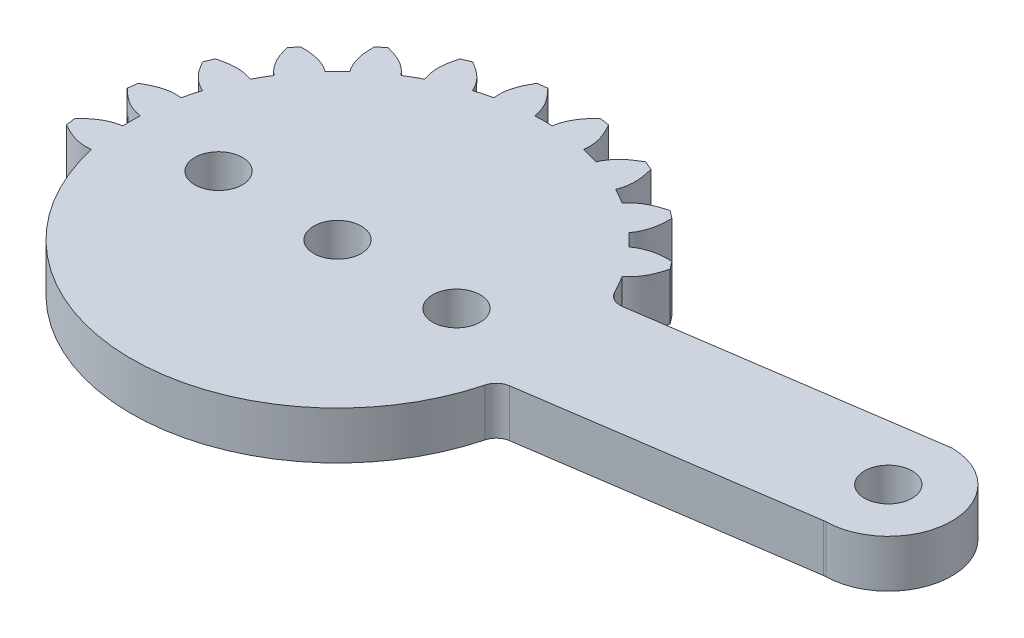
SolidWorks part; units mm, degrees
ref_plane "Front Plane" through (0, 0, 0) normal (0, 0, 1) x (1, 0, 0)
ref_plane "Top Plane" through (0, 0, 0) normal (0, 1, 0) x (1, 0, 0)
ref_plane "Right Plane" through (0, 0, 0) normal (1, 0, 0) x (0, 0, -1)
sketch "Sketch1" plane through (0, 0, 0) normal (0, 1, 0) x (1, 0, 0)
  line L0 (12.6327, 5.3405) -> (30.6525, 7.9886)
  line L1 (0, 0) -> (11.9003, 9.1314) construction
  line L2 (0, 0) -> (19.2179, 25.0452) construction
  line L3 (0, 0) -> (9.1924, 9.1924) construction
  line L5 (30.6617, -0.01) -> (13.4007, -2.5466)
  circle A2 centre (0, 0) radius 1.5
  circle A3 centre (7.5, 0) radius 1.5
  circle A4 centre (-7.5, 0) radius 1.5
  arc A5 (-12.4035, -3.8928) -> (12.5785, -3.2834) centre (0, 0) ccw
  circle A6 centre (30.73, 4) radius 1.5
  arc A8 (11.5954, 5.8777) -> (10.9732, 6.9706) centre (0, 0) ccw
  arc A9 (30.7917, 0.0005) -> (30.8205, 7.999) centre (30.73, 4) ccw
  arc A10 (30.6617, -0.01) -> (30.7917, 0.0005) centre (30.8071, -0.9994) cw
  arc A11 (30.6525, 7.9886) -> (30.8205, 7.999) centre (30.7979, 6.9992) cw
  arc A12 (12.6327, 5.3405) -> (11.5954, 5.8777) centre (12.4873, 6.3299) cw
  arc A13 (12.5785, -3.2834) -> (13.4007, -2.5466) centre (13.5461, -3.536) cw
  spline S0 degree 3 poles (9.5731, 8.7952) (10.2501, 9.2991) (10.982, 9.3793) (11.7091, 9.3754) knots 0 0 0 0 0.58557 0.58557 0.58557 0.58557
  spline S1 degree 2 poles (11.7091, 9.3754) (11.9028, 9.1334) (12.0865, 8.8835) knots 0 0 0 1 1 1
  spline S2 degree 3 poles (10.9732, 6.9706) (11.6352, 7.494) (11.9021, 8.1802) (12.0865, 8.8835) knots 0 0 0 0 0.58557 0.58557 0.58557 0.58557
  spline S4 degree 3 poles (8.7952, 9.5731) (9.2991, 10.2501) (9.3793, 10.982) (9.3754, 11.7091) knots 0 0 0 0 0.58557 0.58557 0.58557 0.58557
  spline S5 degree 2 poles (8.8835, 12.0865) (9.1334, 11.9028) (9.3754, 11.7091) knots 0 0 0 1 1 1
  spline S6 degree 3 poles (6.9706, 10.9732) (7.494, 11.6352) (8.1802, 11.9021) (8.8835, 12.0865) knots 0 0 0 0 0.58557 0.58557 0.58557 0.58557
  spline S7 degree 3 poles (6.0178, 11.5233) (6.3294, 12.3076) (6.2174, 13.0353) (6.0254, 13.7366) knots 0 0 0 0 0.58557 0.58557 0.58557 0.58557
  spline S8 degree 2 poles (5.4526, 13.9739) (5.7415, 13.8612) (6.0254, 13.7366) knots 0 0 0 1 1 1
  spline S9 degree 3 poles (3.893, 12.4034) (4.2273, 13.1783) (4.821, 13.6137) (5.4526, 13.9739) knots 0 0 0 0 0.58557 0.58557 0.58557 0.58557
  spline S10 degree 3 poles (2.8303, 12.6882) (2.9283, 13.5264) (2.6318, 14.2003) (2.2648, 14.828) knots 0 0 0 0 0.58557 0.58557 0.58557 0.58557
  spline S11 degree 2 poles (1.6501, 14.909) (1.9583, 14.8748) (2.2648, 14.828) knots 0 0 0 1 1 1
  spline S12 degree 3 poles (0.5501, 12.9884) (0.6724, 13.8234) (1.1332, 14.3976) (1.6501, 14.909) knots 0 0 0 0 0.58557 0.58557 0.58557 0.58557
  spline S13 degree 3 poles (-0.5501, 12.9884) (-0.6724, 13.8234) (-1.1332, 14.3976) (-1.6501, 14.909) knots 0 0 0 0 0.58557 0.58557 0.58557 0.58557
  spline S14 degree 2 poles (-2.2648, 14.828) (-1.9583, 14.8748) (-1.6501, 14.909) knots 0 0 0 1 1 1
  spline S15 degree 3 poles (-2.8303, 12.6882) (-2.9283, 13.5264) (-2.6318, 14.2003) (-2.2648, 14.828) knots 0 0 0 0 0.58557 0.58557 0.58557 0.58557
  spline S16 degree 3 poles (-3.893, 12.4034) (-4.2273, 13.1783) (-4.821, 13.6137) (-5.4526, 13.9739) knots 0 0 0 0 0.58557 0.58557 0.58557 0.58557
  spline S17 degree 2 poles (-6.0254, 13.7366) (-5.7415, 13.8612) (-5.4526, 13.9739) knots 0 0 0 1 1 1
  spline S18 degree 3 poles (-6.0178, 11.5233) (-6.3294, 12.3076) (-6.2174, 13.0353) (-6.0254, 13.7366) knots 0 0 0 0 0.58557 0.58557 0.58557 0.58557
  spline S19 degree 3 poles (-6.9706, 10.9732) (-7.494, 11.6352) (-8.1802, 11.9021) (-8.8835, 12.0865) knots 0 0 0 0 0.58557 0.58557 0.58557 0.58557
  spline S20 degree 2 poles (-9.3754, 11.7091) (-9.1334, 11.9028) (-8.8835, 12.0865) knots 0 0 0 1 1 1
  spline S21 degree 3 poles (-8.7952, 9.5731) (-9.2991, 10.2501) (-9.3793, 10.982) (-9.3754, 11.7091) knots 0 0 0 0 0.58557 0.58557 0.58557 0.58557
  spline S22 degree 3 poles (-9.5731, 8.7952) (-10.2501, 9.2991) (-10.982, 9.3793) (-11.7091, 9.3754) knots 0 0 0 0 0.58557 0.58557 0.58557 0.58557
  spline S23 degree 2 poles (-12.0865, 8.8835) (-11.9028, 9.1334) (-11.7091, 9.3754) knots 0 0 0 1 1 1
  spline S24 degree 3 poles (-10.9732, 6.9706) (-11.6352, 7.494) (-11.9021, 8.1802) (-12.0865, 8.8835) knots 0 0 0 0 0.58557 0.58557 0.58557 0.58557
  spline S25 degree 3 poles (-11.5233, 6.0178) (-12.3076, 6.3294) (-13.0353, 6.2174) (-13.7366, 6.0254) knots 0 0 0 0 0.58557 0.58557 0.58557 0.58557
  spline S26 degree 2 poles (-13.9739, 5.4526) (-13.8612, 5.7415) (-13.7366, 6.0254) knots 0 0 0 1 1 1
  spline S27 degree 3 poles (-12.4034, 3.893) (-13.1783, 4.2273) (-13.6137, 4.821) (-13.9739, 5.4526) knots 0 0 0 0 0.58557 0.58557 0.58557 0.58557
  spline S28 degree 3 poles (-12.6882, 2.8303) (-13.5264, 2.9283) (-14.2003, 2.6318) (-14.828, 2.2648) knots 0 0 0 0 0.58557 0.58557 0.58557 0.58557
  spline S29 degree 2 poles (-14.909, 1.6501) (-14.8748, 1.9583) (-14.828, 2.2648) knots 0 0 0 1 1 1
  spline S30 degree 3 poles (-12.9884, 0.5501) (-13.8234, 0.6724) (-14.3976, 1.1332) (-14.909, 1.6501) knots 0 0 0 0 0.58557 0.58557 0.58557 0.58557
  spline S31 degree 3 poles (-12.9884, -0.5501) (-13.8234, -0.6724) (-14.3976, -1.1332) (-14.909, -1.6501) knots 0 0 0 0 0.58557 0.58557 0.58557 0.58557
  spline S32 degree 2 poles (-14.828, -2.2648) (-14.8748, -1.9583) (-14.909, -1.6501) knots 0 0 0 1 1 1
  spline S33 degree 3 poles (-12.6882, -2.8303) (-13.5264, -2.9283) (-14.2003, -2.6318) (-14.828, -2.2648) knots 0 0 0 0 0.58557 0.58557 0.58557 0.58557
  spline S34 degree 2 poles (-12.4035, -3.8928) (-12.5684, -3.3677) (-12.6882, -2.8303) knots 0 0 0 0.029411 0.029411 0.029411
  spline S35 degree 3 poles (-12.9884, -0.5501) (-13.0039, -0.1835) (-13.0039, 0.1835) (-12.9884, 0.5501) knots 0.090903 0.090903 0.090903 0.090903 0.120321 0.120321 0.120321 0.120321
  spline S36 degree 3 poles (-12.6882, 2.8303) (-12.6083, 3.1884) (-12.5134, 3.5429) (-12.4034, 3.893) knots 0.181813 0.181813 0.181813 0.181813 0.211231 0.211231 0.211231 0.211231
  spline S37 degree 3 poles (-11.5233, 6.0178) (-11.3535, 6.3431) (-11.17, 6.6609) (-10.9732, 6.9706) knots 0.272722 0.272722 0.272722 0.272722 0.302141 0.302141 0.302141 0.302141
  spline S38 degree 3 poles (-9.5731, 8.7952) (-9.3249, 9.0654) (-9.0654, 9.3249) (-8.7952, 9.5731) knots 0.363632 0.363632 0.363632 0.363632 0.39305 0.39305 0.39305 0.39305
  spline S39 degree 3 poles (-6.9706, 10.9732) (-6.6609, 11.17) (-6.3431, 11.3535) (-6.0178, 11.5233) knots 0.454542 0.454542 0.454542 0.454542 0.48396 0.48396 0.48396 0.48396
  spline S40 degree 3 poles (-3.893, 12.4034) (-3.5429, 12.5134) (-3.1884, 12.6083) (-2.8303, 12.6882) knots 0.545452 0.545452 0.545452 0.545452 0.57487 0.57487 0.57487 0.57487
  spline S41 degree 3 poles (-0.5501, 12.9884) (-0.1835, 13.0039) (0.1835, 13.0039) (0.5501, 12.9884) knots 0.636361 0.636361 0.636361 0.636361 0.665779 0.665779 0.665779 0.665779
  spline S42 degree 3 poles (2.8303, 12.6882) (3.1884, 12.6083) (3.5429, 12.5134) (3.893, 12.4034) knots 0.727271 0.727271 0.727271 0.727271 0.756689 0.756689 0.756689 0.756689
  spline S43 degree 3 poles (6.0178, 11.5233) (6.3431, 11.3535) (6.6609, 11.17) (6.9706, 10.9732) knots 0.818181 0.818181 0.818181 0.818181 0.847599 0.847599 0.847599 0.847599
  spline S44 degree 3 poles (8.7952, 9.5731) (9.0655, 9.3249) (9.325, 9.0653) (9.5731, 8.7952) knots 0.90909 0.90909 0.90909 0.90909 0.938508 0.938508 0.938508 0.938508
  point P32 (30.73, 0)
  point P74 (0, 0)
  point P77 (30.73, 8)
  point P98 (0, 0)
  dimension "D1" = 3
  dimension "D4" = 23.23
  dimension "D5" = 8
  dimension "D15" = 3
  dimension "D7" = 1
  dimension "D2" = 7.5
  dimension "D3" = 15
  dimension "D6" = 4
extrude "Boss-Extrude1" add sketch "Sketch1" along normal blind 3
scale "Scale1" scale about centroid uniform scaling yes scale factor 1.8
